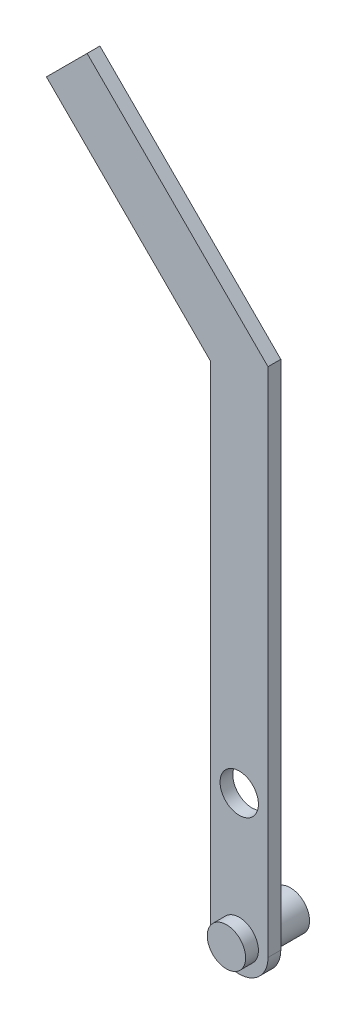
SolidWorks part; units mm, degrees
ref_plane "前视基准面" through (0, 0, 0) normal (0, 0, 1) x (1, 0, 0)
ref_plane "上视基准面" through (0, 0, 0) normal (0, 1, 0) x (1, 0, 0)
ref_plane "右视基准面" through (0, 0, 0) normal (1, 0, 0) x (0, 0, -1)
other "Configuration Table"
sketch "草图1" plane through (0, 0, 0) normal (0, 0, 1) x (1, 0, 0)
  line L0 (0, -20) -> (0, 20) construction
  line L1 (-4.5, -20) -> (-4.5, 20)
  line L2 (4.5, -20) -> (4.5, 20)
  arc A0 (-4.5, -20) -> (4.5, -20) centre (0, -20) ccw
  arc A1 (4.5, 20) -> (-4.5, 20) centre (0, 20) ccw
  circle A2 centre (0, 0) radius 3
  point P2 (0, 0)
extrude "凸台-拉伸1" add sketch "草图1" along normal blind 2
sketch "草图2" plane through (0, 0, 2) normal (0, 0, 1) x (1, 0, 0)
  circle A0 centre (0, -19.8047) radius 3
extrude "凸台-拉伸2" add sketch "草图2" along normal blind 2 and the other way blind 8
sketch "草图3" plane through (0, 0, 2) normal (0, 0, 1) x (1, 0, 0)
  line L0 (-4.5, 20) -> (-4.5, 56.2721)
  line L1 (-4.5, 56.2721) -> (-30.1482, 81.9203)
  line L2 (-30.1482, 81.9203) -> (-23.7843, 88.2843)
  line L3 (-23.7843, 88.2843) -> (4.5, 60)
  line L4 (4.5, 60) -> (4.5, 20)
  line L5 (4.5, 20) -> (-4.5, 20)
  dimension "D1" = 135
  dimension "D2" = 135
  dimension "D3" = 40
  dimension "D4" = 40
extrude "凸台-拉伸4" add sketch "草图3" against normal blind 2
scale "缩放比例1" scale about centroid uniform scaling yes scale factor 3.5
